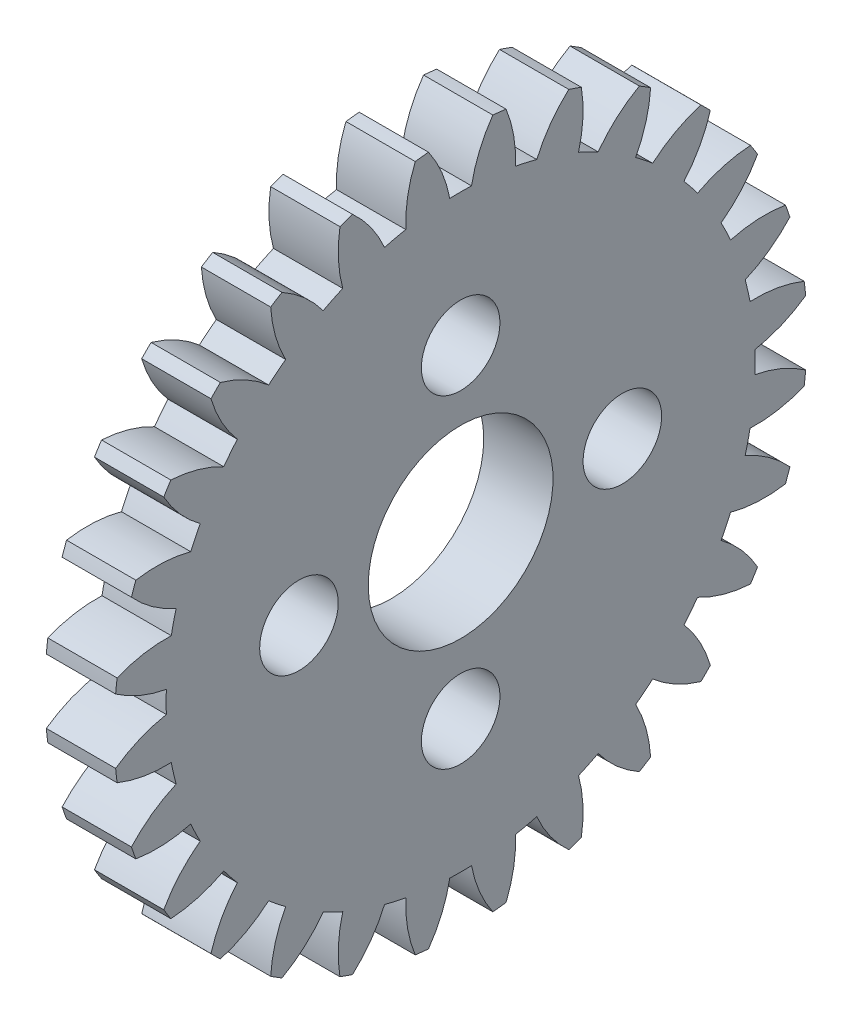
SolidWorks part; units mm, degrees
ref_plane "Plane1" through (0, 0, 0) normal (0, 0, 1) x (1, 0, 0)
ref_plane "Plane2" through (0, 0, 0) normal (0, 1, 0) x (1, 0, 0)
ref_plane "Plane3" through (0, 0, 0) normal (1, 0, 0) x (0, 0, -1)
sketch "HoldingSke" plane through (0, 0, 0) normal (0, 1, 0) x (1, 0, 0)
  line L0 (0, 0) -> (0.8829, -0.4695)
  line L1 (-15, 0) -> (100, 0) construction
  line L2 (0, 0) -> (-2.1039, 2.3779)
  line L3 (0, 0) -> (-11.863, 4.5341)
  line L4 (0, 0) -> (7.6251, 4.0544)
  line L5 (0, 0) -> (-46.8476, -17.4728)
  line L6 (0, 0) -> (-3.3159, -2.2372)
  line L7 (-2.1039, 2.3779) -> (8.6586, 51.2059)
  line L8 (-76.2, 54.61) -> (-75.2, 54.61)
  line L9 (-71.009, 38.7566) -> (-53.1078, 45.2721)
  line L10 (-76.2, 71.12) -> (104.1128, 71.12)
  line L11 (0, 0) -> (-4, 0)
  line L12 (-76.2, 101.6) -> (-76.162, 101.6)
  line L13 (24.9733, 27.94) -> (52.9518, 28.4284)
  line L14 (24.9733, 27.94) -> (24.9743, 27.94)
  line L15 (24.9733, 27.94) -> (100.4006, 29.5858)
  line L16 (-63.627, -1) -> (-12.827, -1)
  circle A0 centre (0, 0) radius 3
  circle A1 centre (0, 0) radius 12.749
  circle A2 centre (0, 0) radius 37.5
  circle A3 centre (0, 0) radius 3
  dimension "MHD" = 25.498
  dimension "Hub_dia" = 75
  dimension "Bore" = 6
  dimension "MBD" = 6
  dimension "Num_teeth" = 28
  dimension "Pitch" = 1
  dimension "Overall_len" = 50
  dimension "Show_teeth" = 28
  dimension "Thickness" = 4
  dimension "OAL" = 50.0001
  dimension "T_dim" = 1
  dimension "Ap" = 20
  dimension "H" = 19.05
  dimension "Pitch_radius" = 180.3128
  dimension "Width" = 4
  dimension "Backlash" = 0.038
  dimension "Addendum_fac" = 1
  dimension "Dedendum_fac" = 1.25
  dimension "Clearance_fac" = 0.25
  dimension "Dedendum_add" = 0.001
  dimension "Module" = 1
sketch "BasProSke" plane through (0, 0, 0) normal (0, 1, 0) x (1, 0, 0)
  line L0 (-10, 0) -> (60, 0) construction
  line L1 (0, 0) -> (0, 15)
  line L2 (0, 0) -> (3, 0)
  line L3 (3, 0) -> (3, 15)
  line L4 (3, 15) -> (0, 15)
  dimension "Thickness" = 3
  dimension "Diameter" = 30
revolve "Base-Revolve" add sketch "BasProSke" angle 360 about L0
sketch "TooCutSke" plane through (0, 0, 0) normal (1, 0, 0) x (0, 0, -1)
  line L1 (0, 0) -> (0, 107) construction
  line L2 (0, 0) -> (-0.8515, 13.9741) construction
  line L3 (0, 0) -> (-3.1309, 27.7873) construction
  line L4 (-0.8515, 13.9741) -> (-1.5654, 13.8936) construction
  arc A0 (0.4713, 12.7403) -> (-0.4713, 12.7403) centre (0, 0) ccw
  arc A1 (1.4098, 14.9591) -> (-1.4098, 14.9591) centre (0, 0) ccw
  circle A2 centre (0, 0) radius 14 construction
  circle A3 centre (0, 0) radius 13.1557 construction
  arc A4 (-0.4713, 12.7403) -> (-1.4098, 14.9591) centre (-5.9775, 11.7193) ccw
  arc A5 (1.4098, 14.9591) -> (0.4713, 12.7403) centre (5.9775, 11.7193) ccw
  dimension "Root_dia" = 25.498
  dimension "Overcut_dia" = 30.0508
  dimension "Pitch_dia" = 28
  dimension "Base_dia" = 26.3114
  dimension "Flank_rad" = 5.6
  dimension "Half_ang" = 6.429
  dimension "Half_CT" = 0.7185
extrude "ToothCut" cut sketch "TooCutSke" along normal through all
fillet "Breaks" [suppressed] radius 0.02
fillet "RootFillets" [suppressed] radius 0.251
pattern_circular "TeethCuts" count 28 every 12.857 about axis through (-10, 0, 0) along (1, 0, 0) of "ToothCut", "RootFillets", "Breaks"
sketch "HubNeaOneSke" plane through (0, 0, 0) normal (-1, 0, 0) x (0, 0, 1)
  circle A0 centre (0, 0) radius 12.749
  dimension "Diameter" = 25.498
extrude "HubNearOne" [suppressed] add sketch "HubNeaOneSke" along normal blind 47.0001
sketch "HubNeaBotSke" plane through (0, 0, 0) normal (-1, 0, 0) x (0, 0, 1)
  circle A0 centre (0, 0) radius 12.749
  dimension "Diameter" = 25.498
extrude "HubNearBoth" [suppressed] add sketch "HubNeaBotSke" along normal blind 23.5
ref_plane "FarPln" through (3, 0, 0) normal (1, 0, 0) x (0, 0, -1)
sketch "HubFarSke" plane through (3, 0, 0) normal (1, 0, 0) x (0, 0, -1)
  circle A0 centre (0, 0) radius 12.749
  dimension "Diameter" = 25.498
extrude "HubFar" [suppressed] add sketch "HubFarSke" along normal blind 23.5
sketch "BorSke" plane through (0, 0, 0) normal (1, 0, 0) x (0, 0, -1)
  circle A0 centre (0, 0) radius 4
  dimension "Diameter" = 8
extrude "Bore" cut sketch "BorSke" along normal mid plane 100.0001
sketch "KeySke" plane through (0, 0, 0) normal (1, 0, 0) x (0, 0, -1)
  line L0 (-1, 0) -> (-1, 4)
  line L1 (-1, 4) -> (1, 4)
  line L2 (1, 4) -> (1, 0)
  line L3 (0, 0) -> (0, 34) construction
  line L4 (-1, 0) -> (1, 0)
  dimension "Offset" = 4
  dimension "Width" = 2
extrude "Keyway" [suppressed] cut sketch "KeySke" along normal mid plane 100.0001
pattern_circular "Keyway2" [suppressed] count 2 every 90 about axis through (-10, 0, 0) along (1, 0, 0)
hole_wizard "M3 Clearance Hole1" positions "Sketch1" profile "Sketch2" hole size "M3" standard "ANSI Metric" end condition through all
sketch "Sketch1" plane through (3, 0, 0) normal (1, 0, 0) x (0, 0, -1)
  line L0 (0, 0) -> (0, 7) construction
  point P2 (0, 7)
  dimension "D1" = 7
sketch "Sketch2" plane through (3, 7, 0) normal (0, 1, 0) x (0, 0, -1)
  line L0 (0, 0) -> (0, 3)
  line L1 (0, 3) -> (1.7, 3)
  line L2 (1.7, 3) -> (1.7, 0)
  line L5 (1.7, 0) -> (0, 0)
  line L11 (0, -6.35) -> (0, 107.95) construction
  dimension "Thru Hole Dia." = 3.4
  dimension "Thru Hole Depth" = 3
pattern_circular "CirPattern1" count 4 over 360 about axis through (0, 0, 0) along (1, 0, 0) of "M3 Clearance Hole1"
equation "' \"Module@HoldingSke\" = 6.35"
equation "' \"Num_teeth@HoldingSke\" = 12"
equation "' \"Ap@HoldingSke\" =  20"
equation "' \"Ap@HoldingSke\" = 20"
equation "' \"Width@HoldingSke\" = 0.5 * 25.4"
equation "' \"Hub_dia@HoldingSke\"= 1 * 25.4"
equation "' \"Hub_dia@HoldingSke\" = 1 * 25.4"
equation "' \"Overall_len@HoldingSke\" = 1.0 * 25.4"
equation "' \"Bore@HoldingSke\" = 0.75 * 25.4"
equation "' \"T_dim@HoldingSke\" = 0.1 * 25.4"
equation "' \"Width@KeySke\" = 0.25 * 25.4"
equation "' \"Show_teeth@HoldingSke\" = 13"
equation "' \"Backlash@HoldingSke\" = 0.009 * 25.4"
equation "' \"Addendum_fac@HoldingSke\" = 1.0"
equation "' \"Dedendum_fac@HoldingSke\" = 1.25"
equation "' \"Dedendum_add@HoldingSke\" = 0.00005 * 25.4"
equation "' \"Clearance_fac@HoldingSke\" = 0.25"
equation "\"Pitch@HoldingSke\" = 1 / \"Module@HoldingSke\""
equation "\"Overcut_dia@TooCutSke\" = (\"Num_teeth@HoldingSke\" + 2 * \"Addendum_fac@HoldingSke\") / \"Pitch@HoldingSke\" + 0.002 * 25.4"
equation "\"Pitch_dia@TooCutSke\" = \"Num_teeth@HoldingSke\" / \"Pitch@HoldingSke\""
equation "\"Base_dia@TooCutSke\" = \"Num_teeth@HoldingSke\" / \"Pitch@HoldingSke\" * cos((\"Ap@HoldingSke\"  * 3.14159265 / 180))"
equation "\"Root_dia@TooCutSke\" = (\"Num_teeth@HoldingSke\" + 2) / \"Pitch@HoldingSke\" - 2 * (\"Addendum_fac@HoldingSke\" + \"Dedendum_fac@HoldingSke\") / \"Pitch@HoldingSke\" - \"Dedendum_add@HoldingSke\" * 2"
equation "\"Half_ang@TooCutSke\" = 180 / \"Num_teeth@HoldingSke\""
equation "\"Half_CT@TooCutSke\" = \"Num_teeth@HoldingSke\" / \"Pitch@HoldingSke\" * sin((3.14159265 / 2 / \"Num_teeth@HoldingSke\")) / 2 - 7 * \"Backlash@HoldingSke\" / 4"
equation "\"Flank_rad@TooCutSke\" = \"Num_teeth@HoldingSke\" / \"Pitch@HoldingSke\" / 5"
equation "\"Radius@RootFillets\" = \"Clearance_fac@HoldingSke\" / \"Pitch@HoldingSke\" + \"Dedendum_add@HoldingSke\""
equation "\"Break_rad@Breaks\" = 0.02 / \"Pitch@HoldingSke\""
equation "\"Thickness@HoldingSke\" = \"Width@HoldingSke\""
equation "\"OAL@HoldingSke\" = \"Thickness@HoldingSke\""
equation "\"MHD@HoldingSke\" = (\"Num_teeth@HoldingSke\" + 2) / \"Pitch@HoldingSke\" - 2 * (\"Addendum_fac@HoldingSke\" + \"Dedendum_fac@HoldingSke\")  / \"Pitch@HoldingSke\" - \"Dedendum_add@HoldingSke\" * 2"
equation "\"MBD@HoldingSke\" = (\"Num_teeth@HoldingSke\" + 2) / \"Pitch@HoldingSke\" - 2 * (\"Addendum_fac@HoldingSke\" + \"Dedendum_fac@HoldingSke\")  / \"Pitch@HoldingSke\" - \"Dedendum_add@HoldingSke\" * 2 - 0.002 * 25.4"
equation "\"MHD@HoldingSke\" = ((sgn( \"MHD@HoldingSke\" - \"Hub_dia@HoldingSke\" )-1)*( \"MHD@HoldingSke\" - \"Hub_dia@HoldingSke\" ))/-2+ \"Hub_dia@HoldingSke\""
equation "\"MBD@HoldingSke\" = ((sgn( \"MBD@HoldingSke\" - \"Bore@HoldingSke\" )-1)*( \"MBD@HoldingSke\" - \"Bore@HoldingSke\" ))/-2+ \"Bore@HoldingSke\""
equation "\"OAL@HoldingSke\" = ((sgn( \"OAL@HoldingSke\" - \"Overall_len@HoldingSke\" )+1)*( \"OAL@HoldingSke\" - \"Overall_len@HoldingSke\" ))/2 + \"Overall_len@HoldingSke\" + 0.000002 * 25.4"
equation "\"Num_teeth@TeethCuts\" = int( \"Show_teeth@HoldingSke\" ) + 1"
equation "\"Num_teeth@TeethCuts\" = ((sgn( \"Num_teeth@TeethCuts\" - \"Num_teeth@HoldingSke\" )-1)*( \"Num_teeth@TeethCuts\" - \"Num_teeth@HoldingSke\" ))/-2+ \"Num_teeth@HoldingSke\""
equation "\"Num_teeth@TeethCuts\" = ((sgn( \"Num_teeth@TeethCuts\" - 2.0)+1)*( \"Num_teeth@TeethCuts\" - 2.0))/2 +2.0"
equation "\"Angle@TeethCuts\" = 360.0 / \"Num_teeth@HoldingSke\""
equation "\"Diameter@BasProSke\" = (\"Num_teeth@HoldingSke\" + 2 * \"Addendum_fac@HoldingSke\") / \"Pitch@HoldingSke\""
equation "' \"Fillet_rad@BasProSke\" =  \"Thickness@HoldingSke\" * 0.05"
equation "' \"Fillet_rad@BasProSke\" = \"Thickness@HoldingSke\" * 0.05"
equation "\"MHD@HoldingSke\" = ((sgn( \"MHD@HoldingSke\" - \"Root_dia@TooCutSke\" )-1)*( \"MHD@HoldingSke\" - \"Root_dia@TooCutSke\" ))/-2+ \"Root_dia@TooCutSke\""
equation "\"Diameter@HubNeaOneSke\" = \"MHD@HoldingSke\""
equation "\"Length@HubNearOne\" = \"OAL@HoldingSke\" - \"Thickness@BasProSke\""
equation "\"Diameter@HubNeaBotSke\" = \"MHD@HoldingSke\""
equation "\"Length@HubNearBoth\" = ( \"OAL@HoldingSke\" - \"Thickness@BasProSke\" ) / 2.0"
equation "\"Thickness@FarPln\" = \"Thickness@BasProSke\""
equation "\"Diameter@HubFarSke\" = \"MHD@HoldingSke\""
equation "\"Length@HubFar\" = ( \"OAL@HoldingSke\" - \"Thickness@BasProSke\" ) / 2.0"
equation "\"D1@Bore\" = \"OAL@HoldingSke\" * 2.0"
equation "\"D1@Keyway\" = \"OAL@HoldingSke\" * 2.0"
equation "\"Offset@KeySke\" = \"T_dim@HoldingSke\" + \"MBD@HoldingSke\" / 2.0"
